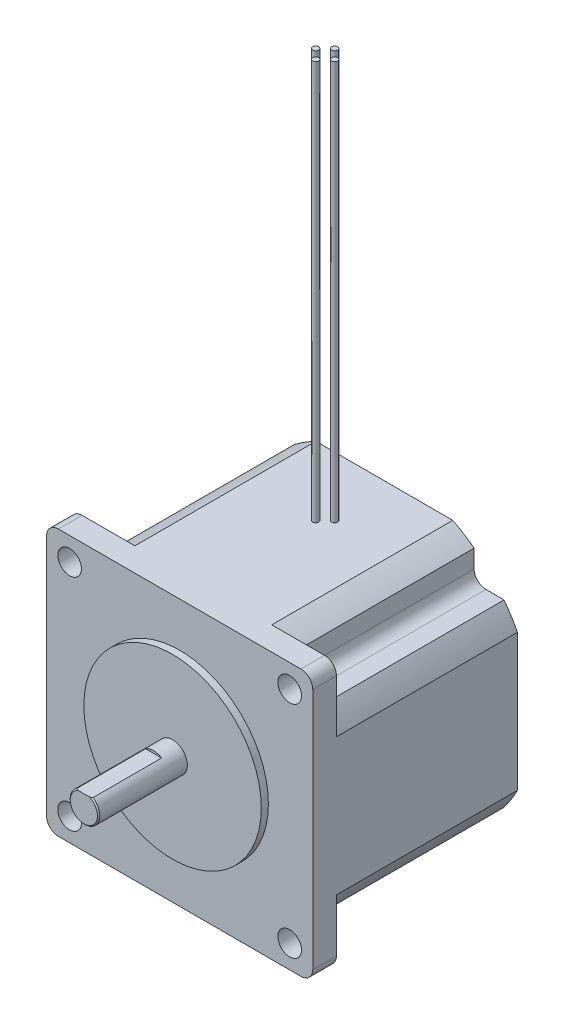
SolidWorks part; units mm, degrees
ref_plane "Plan de face" through (0, 0, 0) normal (0, 0, 1) x (1, 0, 0)
ref_plane "Plan de dessus" through (0, 0, 0) normal (0, 1, 0) x (1, 0, 0)
ref_plane "Plan de droite" through (0, 0, 0) normal (1, 0, 0) x (0, 0, -1)
ref_plane "Plan1" through (0, 0, 43.942) normal (0, 0, 1) x (1, 0, 0)
sketch "Esquisse1" plane through (0, 0, 43.942) normal (0, 0, 1) x (1, 0, 0)
  line L0 (28.575, -28.575) -> (28.575, 28.575)
  line L1 (28.575, 28.575) -> (-28.575, 28.575)
  line L2 (-28.575, 28.575) -> (-28.575, -28.575)
  line L3 (-28.575, -28.575) -> (28.575, -28.575)
extrude "Boss.-Extru.1" add sketch "Esquisse1" against normal blind 43.942
sketch "Esquisse2" plane through (0, 0, 0) normal (0, 0, -1) x (-1, 0, 0)
  line L0 (-28.575, -28.575) -> (-14.6925, -28.575)
  line L1 (-28.575, -14.6925) -> (-28.575, -28.575)
  arc A0 (-14.6925, -28.575) -> (-28.575, -14.6925) centre (0, 0) cw
extrude "Enlèv. mat.-Extru.1" cut sketch "Esquisse2" against normal blind 38.862
sketch "Esquisse3" plane through (0, 0, 0) normal (0, 0, -1) x (-1, 0, 0)
  line L0 (-19.2786, -25.7048) -> (-19.2786, -19.2786)
  line L1 (-19.2786, -19.2786) -> (-25.7048, -19.2786)
  arc A0 (-25.7048, -19.2786) -> (-19.2786, -25.7048) centre (0, 0) ccw
extrude "Enlèv. mat.-Extru.2" cut sketch "Esquisse3" against normal blind 38.862
sketch "Esquisse4" plane through (0, 0, 0) normal (0, 0, -1) x (-1, 0, 0)
  line L0 (-28.575, 28.575) -> (-28.575, 14.6925)
  line L1 (-14.6925, 28.575) -> (-28.575, 28.575)
  arc A0 (-28.575, 14.6925) -> (-14.6925, 28.575) centre (0, 0) cw
extrude "Enlèv. mat.-Extru.3" cut sketch "Esquisse4" against normal blind 38.862
sketch "Esquisse5" plane through (0, 0, 0) normal (0, 0, -1) x (-1, 0, 0)
  line L0 (-25.7048, 19.2786) -> (-19.2786, 19.2786)
  line L1 (-19.2786, 19.2786) -> (-19.2786, 25.7048)
  arc A0 (-19.2786, 25.7048) -> (-25.7048, 19.2786) centre (0, 0) ccw
extrude "Enlèv. mat.-Extru.4" cut sketch "Esquisse5" against normal blind 38.862
sketch "Esquisse6" plane through (0, 0, 0) normal (0, 0, -1) x (-1, 0, 0)
  line L0 (28.575, 28.575) -> (14.6925, 28.575)
  line L1 (28.575, 14.6925) -> (28.575, 28.575)
  arc A0 (14.6925, 28.575) -> (28.575, 14.6925) centre (0, 0) cw
extrude "Enlèv. mat.-Extru.5" cut sketch "Esquisse6" against normal blind 38.862
sketch "Esquisse7" plane through (0, 0, 0) normal (0, 0, -1) x (-1, 0, 0)
  line L0 (19.2786, 25.7048) -> (19.2786, 19.2786)
  line L1 (19.2786, 19.2786) -> (25.7048, 19.2786)
  arc A0 (25.7048, 19.2786) -> (19.2786, 25.7048) centre (0, 0) ccw
extrude "Enlèv. mat.-Extru.6" cut sketch "Esquisse7" against normal blind 38.862
sketch "Esquisse8" plane through (0, 0, 0) normal (0, 0, -1) x (-1, 0, 0)
  line L0 (28.575, -28.575) -> (28.575, -14.6925)
  line L1 (14.6925, -28.575) -> (28.575, -28.575)
  arc A0 (28.575, -14.6925) -> (14.6925, -28.575) centre (0, 0) cw
extrude "Enlèv. mat.-Extru.7" cut sketch "Esquisse8" against normal blind 38.862
sketch "Esquisse9" plane through (0, 0, 0) normal (0, 0, -1) x (-1, 0, 0)
  line L0 (25.7048, -19.2786) -> (19.2786, -19.2786)
  line L1 (19.2786, -19.2786) -> (19.2786, -25.7048)
  arc A0 (19.2786, -25.7048) -> (25.7048, -19.2786) centre (0, 0) ccw
extrude "Enlèv. mat.-Extru.8" cut sketch "Esquisse9" against normal blind 38.862
sketch "Esquisse10" plane through (0, 0, 43.942) normal (0, 0, 1) x (1, 0, 0)
  circle A0 centre (0, 0) radius 19.05
extrude "Boss.-Extru.2" add sketch "Esquisse10" along normal blind 1.524
sketch "Esquisse11" plane through (0, 0, 45.466) normal (0, 0, 1) x (1, 0, 0)
  circle A0 centre (0, 0) radius 3.175
extrude "Boss.-Extru.3" add sketch "Esquisse11" along normal blind 19.05
sketch "Esquisse12" plane through (0, 0, 64.516) normal (0, 0, 1) x (1, 0, 0)
  line L0 (-1.7227, 2.667) -> (1.7227, 2.667)
  arc A0 (1.7227, 2.667) -> (-1.7227, 2.667) centre (0, 0) ccw
extrude "Enlèv. mat.-Extru.9" cut sketch "Esquisse12" against normal blind 14.986
ref_plane "Plan2" through (0, 0, 12.7) normal (0, 0, -1) x (-1, 0, 0)
sketch "Esquisse13" plane through (0, 0, 12.7) normal (0, 0, -1) x (-1, 0, 0)
  line L0 (1.397, 28.575) -> (2.032, 28.575)
  line L1 (2.032, 28.575) -> (2.032, 114.3)
  line L2 (2.032, 114.3) -> (1.397, 114.3)
  line L3 (1.397, 114.3) -> (1.397, 28.575)
  line L4 (2.032, 28.575) -> (2.032, 114.3) construction
revolve "Révolution1" add sketch "Esquisse13" angle 360 about L4
sketch "Esquisse14" plane through (0, 0, 12.7) normal (0, 0, -1) x (-1, 0, 0)
  line L0 (-2.667, 28.575) -> (-2.032, 28.575)
  line L1 (-2.032, 28.575) -> (-2.032, 114.3)
  line L2 (-2.032, 114.3) -> (-2.667, 114.3)
  line L3 (-2.667, 114.3) -> (-2.667, 28.575)
  line L4 (-2.032, 28.575) -> (-2.032, 114.3) construction
revolve "Révolution2" add sketch "Esquisse14" angle 360 about L4
ref_plane "Plan3" through (0, 0, 14.732) normal (0, 0, -1) x (-1, 0, 0)
sketch "Esquisse15" plane through (0, 0, 14.732) normal (0, 0, -1) x (-1, 0, 0)
  line L0 (-0.635, 28.575) -> (0, 28.575)
  line L1 (0, 28.575) -> (0, 114.3)
  line L2 (0, 114.3) -> (-0.635, 114.3)
  line L3 (-0.635, 114.3) -> (-0.635, 28.575)
  line L4 (0, 28.575) -> (0, 114.3) construction
revolve "Révolution3" add sketch "Esquisse15" angle 360 about L4
ref_plane "Plan4" through (0, 0, 10.668) normal (0, 0, -1) x (-1, 0, 0)
sketch "Esquisse16" plane through (0, 0, 10.668) normal (0, 0, -1) x (-1, 0, 0)
  line L0 (-0.635, 28.575) -> (0, 28.575)
  line L1 (0, 28.575) -> (0, 114.3)
  line L2 (0, 114.3) -> (-0.635, 114.3)
  line L3 (-0.635, 114.3) -> (-0.635, 28.575)
  line L4 (0, 28.575) -> (0, 114.3) construction
revolve "Révolution4" add sketch "Esquisse16" angle 360 about L4
hole_wizard "Perçage1" positions "Esquisse18" profile "Esquisse17" legacy
sketch "Esquisse18" plane through (0, 0, 38.862) normal (0, 0, -1) x (-1, 0, 0)
  point P0 (-23.622, -23.622)
  point P1 (-23.622, 23.622)
  point P2 (23.622, 23.622)
  point P3 (23.622, -23.622)
sketch "Esquisse17" plane through (23.622, -23.622, 38.862) normal (1, 0, 0) x (0, 1, 0)
  line L0 (0, 0) -> (0, 25.654)
  line L1 (0, 25.654) -> (2.54, 25.654)
  line L2 (2.54, 25.654) -> (2.54, 0)
  line L3 (2.54, 0) -> (0, 0)
  line L4 (0, 110) -> (0, -10) construction
  dimension "Diamètre" = 5.08
  dimension "Profondeur" = 25.654
chamfer "Chanfrein1" distance 0.254 angle 45 1 edges at (0, -3.175, 64.516)
fillet "Congé1" radius 2.54 8 edges at (-19.2786, -19.2786, 19.431) (19.2786, 19.2786, 19.431) (19.2786, -19.2786, 19.431) (28.575, -28.575, 41.402) (-19.2786, 19.2786, 19.431) (28.575, 28.575, 41.402) (-28.575, -28.575, 41.402) (-28.575, 28.575, 41.402)
